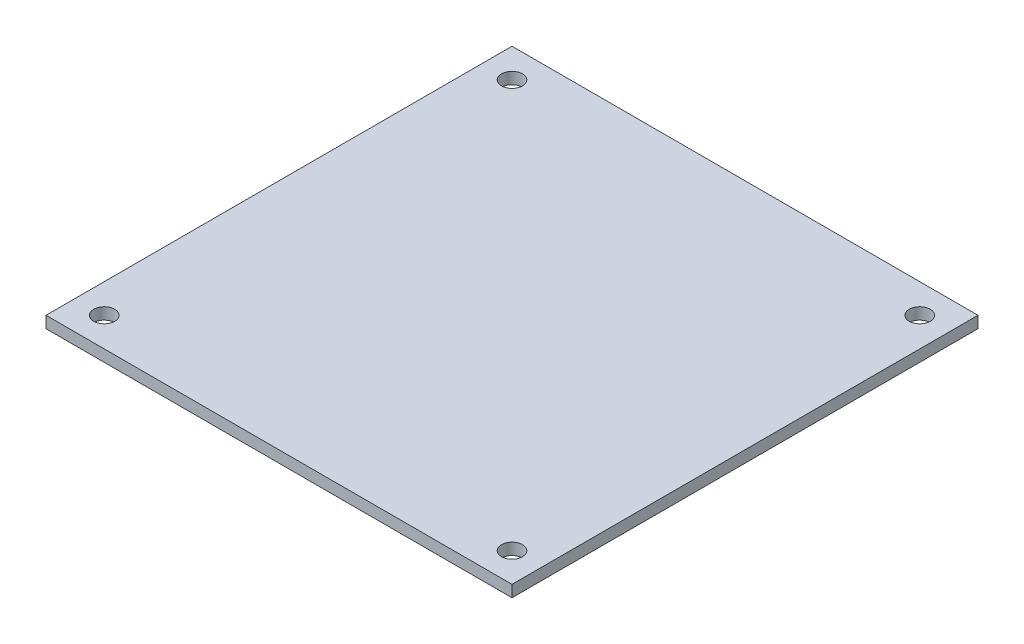
SolidWorks part; units mm, degrees
ref_plane "Front Plane" through (0, 0, 0) normal (0, 0, 1) x (1, 0, 0)
ref_plane "Top Plane" through (0, 0, 0) normal (0, 1, 0) x (1, 0, 0)
ref_plane "Right Plane" through (0, 0, 0) normal (1, 0, 0) x (0, 0, -1)
sketch "Sketch1" plane through (0, 0, 0) normal (0, 1, 0) x (1, 0, 0)
  line L1 (0, 0) -> (80, 0)
  line L2 (0, 0) -> (0, 80)
  line L3 (0, 80) -> (80, 80)
  line L4 (80, 0) -> (80, 80)
  dimension "D1" = 80
  dimension "D2" = 80
extrude "PCB" add sketch "Sketch1" along normal blind 2
sketch "Sketch2" plane through (0, 2, 0) normal (0, 1, 0) x (1, 0, 0)
  line L0 (80, 80) -> (0, 80) construction
  line L1 (0, 80) -> (0, 0) construction
  circle A0 centre (5, 75) radius 1.8
  dimension "D1" = 3.6
  dimension "D2" = 5
  dimension "D3" = 5
extrude "Attachment Holes" cut sketch "Sketch2" against normal through all
pattern_linear "LPattern1" count 2 spacing 70 along (1, 0, 0) count 2 spacing 70 along (0, 0, 1) of "Attachment Holes"
